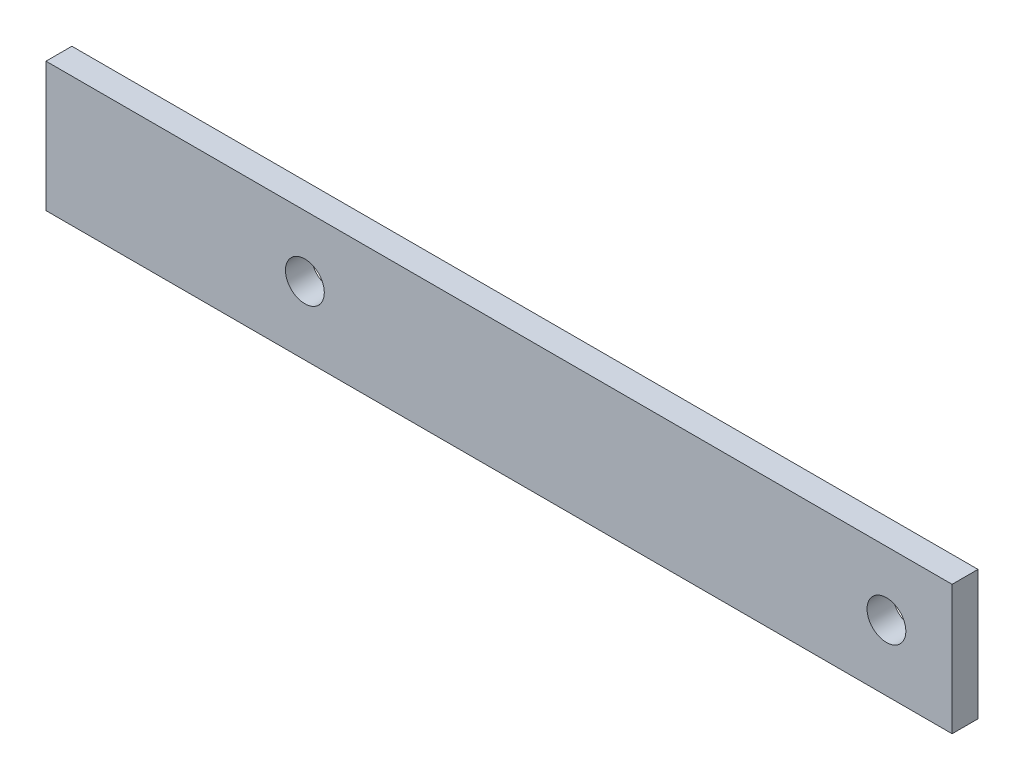
SolidWorks part; units mm, degrees
ref_plane "Front Plane" through (0, 0, 0) normal (0, 0, 1) x (1, 0, 0)
ref_plane "Top Plane" through (0, 0, 0) normal (0, 1, 0) x (1, 0, 0)
ref_plane "Right Plane" through (0, 0, 0) normal (1, 0, 0) x (0, 0, -1)
sketch "Sketch1" plane through (0, 0, 0) normal (0, 0, 1) x (1, 0, 0)
  line L1 (-70, 0) -> (0, 0)
  line L2 (-70, 0) -> (-70, -10)
  line L3 (-70, -10) -> (0, -10)
  line L4 (0, 0) -> (0, -10)
  dimension "D1" = 70
  dimension "D2" = 10
extrude "Boss-Extrude1" add sketch "Sketch1" along normal blind 2
sketch "Sketch2" plane through (0, 0, 2) normal (0, 0, 1) x (1, 0, 0)
  circle A0 centre (-5.0736, -4.9286) radius 1.5
  dimension "D1" = 3
extrude "Cut-Extrude1" cut sketch "Sketch2" against normal blind 2 contours A0
sketch "Sketch3" plane through (0, 0, 2) normal (0, 0, 1) x (1, 0, 0)
  line L0 (-70, 0) -> (-70, -10) construction
  circle A0 centre (-50, -4.7332) radius 1.5
  point P2 (0, 0)
  point P3 (0, 0)
  point P4 (-65.5084, -4.7332)
  dimension "D1" = 3
  dimension "D2" = 20
extrude "Cut-Extrude2" cut sketch "Sketch3" against normal blind 10
